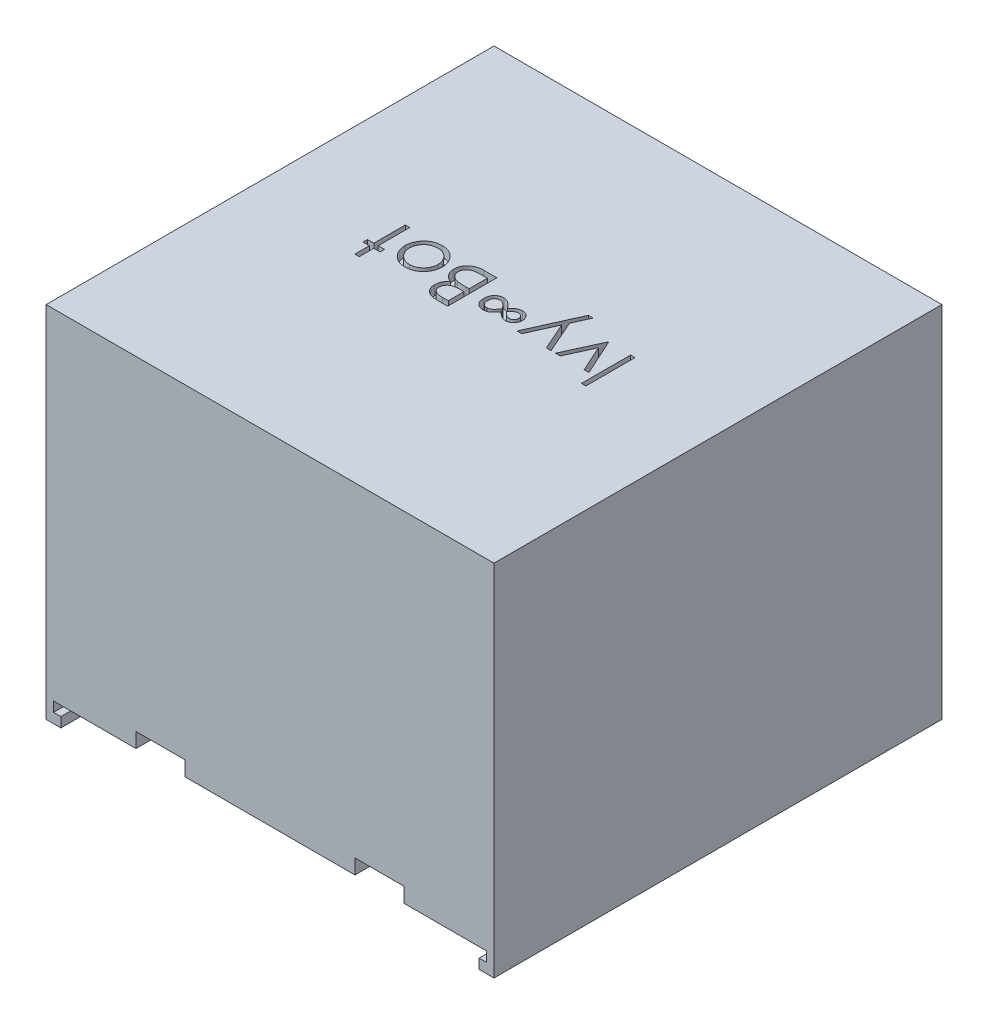
SolidWorks part; units mm, degrees
ref_plane "Front Plane" through (0, 0, 0) normal (0, 0, 1) x (1, 0, 0)
ref_plane "Top Plane" through (0, 0, 0) normal (0, 1, 0) x (1, 0, 0)
ref_plane "Right Plane" through (0, 0, 0) normal (1, 0, 0) x (0, 0, -1)
sketch "Sketch1" plane through (0, 0, 0) normal (0, 1, 0) x (1, 0, 0)
  line L0 (-45.5, 45.5) -> (45.5, 45.5)
  line L1 (-42.5, -42.5) -> (42.5, -42.5)
  line L2 (-42.5, -42.5) -> (-42.5, 42.5)
  line L3 (-42.5, 42.5) -> (42.5, 42.5)
  line L4 (42.5, -42.5) -> (42.5, 42.5)
  line L5 (-42.5, -42.5) -> (42.5, 42.5) construction
  line L6 (-42.5, 42.5) -> (42.5, -42.5) construction
  line L11 (45.5, -45.5) -> (45.5, 45.5)
  line L12 (-45.5, -45.5) -> (45.5, -45.5)
  line L13 (-45.5, -45.5) -> (-45.5, 45.5)
  point P0 (0, 0)
  dimension "D2" = 85
  dimension "D1" = 3
extrude "Boss-Extrude1" add sketch "Sketch1" along normal blind 70
sketch "Sketch2" plane through (0, 70, 0) normal (0, 1, 0) x (1, 0, 0)
  line L1 (-45.5, -45.5) -> (45.5, -45.5)
  line L2 (-45.5, -45.5) -> (-45.5, 45.5)
  line L3 (-45.5, 45.5) -> (45.5, 45.5)
  line L4 (45.5, -45.5) -> (45.5, 45.5)
extrude "Boss-Extrude2" add sketch "Sketch2" along normal blind 3
sketch "Sketch4" plane through (0, 0, 45.5) normal (0, 0, 1) x (1, 0, 0)
  line L0 (-45.5, 73) -> (-45.5, 0) construction
  line L1 (-44, 2) -> (44, 2)
  line L2 (-44, 2) -> (-44, 4)
  line L3 (-44, 4) -> (44, 4)
  line L4 (44, 2) -> (44, 4)
  line L5 (45.5, 73) -> (45.5, 0) construction
  line L6 (-45.5, 0) -> (45.5, 0) construction
  dimension "D1" = 1.5
  dimension "D2" = 1.5
  dimension "D3" = 2
  dimension "D4" = 2
extrude "Cut-Extrude1" cut sketch "Sketch4" against normal offset from surface (89 mm away) 2 up to face at (0, 36.5, -45.5)
sketch "Sketch5" plane through (0, 0, 45.5) normal (0, 0, 1) x (1, 0, 0)
  line L0 (-45.5, 0) -> (45.5, 0) construction
  line L1 (-42.5, 2) -> (42.5, 2)
  line L2 (-42.5, 2) -> (-42.5, 0)
  line L3 (-42.5, 0) -> (42.5, 0)
  line L4 (42.5, 2) -> (42.5, 0)
  line L5 (42.5, 2) -> (42.5, 0) construction
extrude "Cut-Extrude2" cut sketch "Sketch5" against normal up to next
sketch "Sketch6" plane through (0, 0, -45.5) normal (0, 0, -1) x (-1, 0, 0)
  line L0 (-20, 55) -> (20, 55) construction
  line L1 (-45.5, 0) -> (45.5, 0) construction
  line L2 (-28.0304, 21.4645) -> (-24.4949, 25)
  line L3 (28.0304, 21.4645) -> (24.4949, 25)
  circle A0 centre (-20, 55) radius 7.5
  circle A1 centre (20, 55) radius 7.5
  arc A2 (-24.4949, 25) -> (24.4949, 25) centre (0, 50) ccw
  arc A3 (-28.0304, 21.4645) -> (28.0304, 21.4645) centre (0, 50) ccw
  circle A4 centre (0, 35.36) radius 4
  point P4 (0, 55)
  point P12 (0, 35.36)
  point P14 (0, 0)
  point P17 (0, 0)
  point P18 (0, 0)
  point P19 (-21.2901, 22.1716)
  point P20 (21.8949, 22.1716)
  point P21 (-27.3965, 21.4645)
  dimension "D1" = 15
  dimension "D6" = 35
  dimension "D9" = 8
  dimension "D2" = 40
  dimension "D3" = 55
  dimension "D4" = 315
  dimension "D5" = 5
  dimension "D7" = 50
  dimension "D10" = 25
extrude "Cut-Extrude3" cut sketch "Sketch6" against normal up to next
sketch "Sketch7" plane through (0, 0, 45.5) normal (0, 0, 1) x (1, 0, 0)
  line L0 (44, 4) -> (-44, 4) construction
  line L1 (-27.25, 4) -> (-17.25, 4)
  line L2 (-27.25, 4) -> (-27.25, 7)
  line L3 (-27.25, 7) -> (-17.25, 7)
  line L4 (-17.25, 4) -> (-17.25, 7)
  line L5 (-17.25, 7) -> (17.25, 7) construction
  line L6 (17.25, 4) -> (27.25, 4)
  line L7 (17.25, 4) -> (17.25, 7)
  line L8 (17.25, 7) -> (27.25, 7)
  line L9 (27.25, 4) -> (27.25, 7)
  point P10 (0, 7)
  point P11 (-25, 6.1843)
  dimension "D1" = 10
  dimension "D2" = 10
  dimension "D3" = 34.5
  dimension "D4" = 3
extrude "Cut-Extrude4" cut sketch "Sketch7" against normal up to next
sketch "Sketch8" plane through (0, 73, 0) normal (0, 1, 0) x (1, 0, 0)
  line L0 (27.7497, 5) -> (-27.7497, 5) construction
  line L1 (45.5, -45.5) -> (45.5, 45.5) construction
  text T0 "Ivy∞Bot\r\n" font "Century Gothic" height 10
  point P5 (45.5, 0)
  point P7 (0, 5)
  dimension "D1" = 5
extrude "Cut-Extrude5" cut sketch "Sketch8" against normal blind 2
